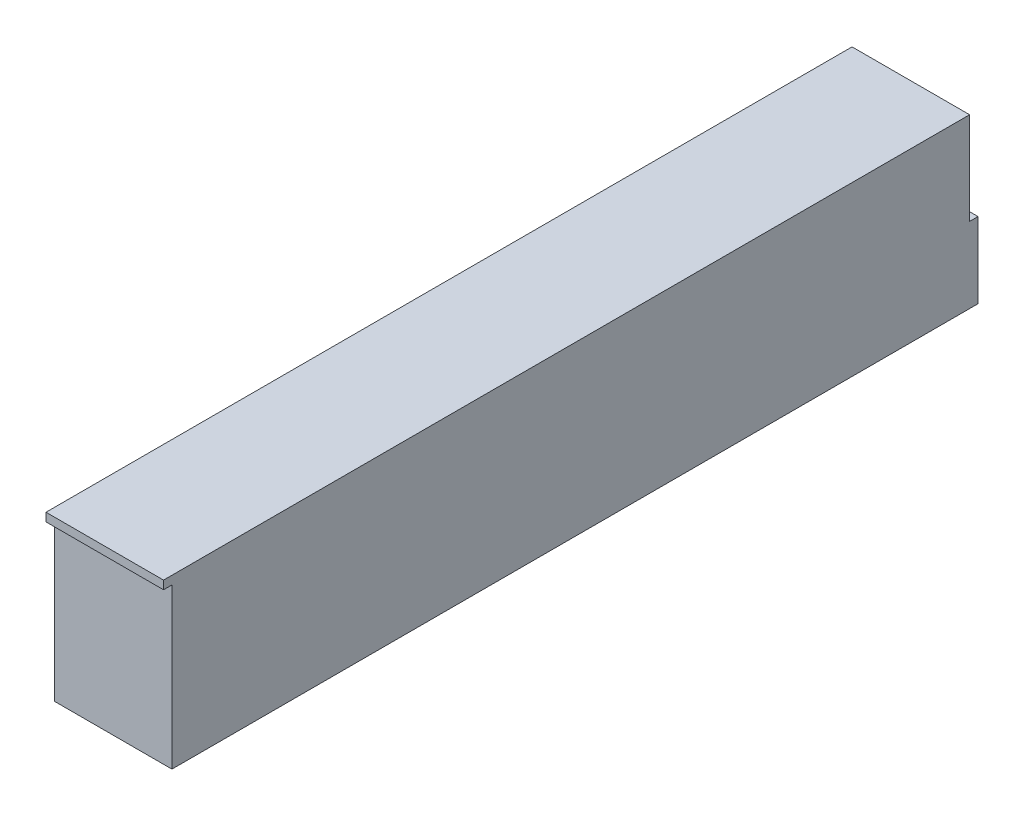
SolidWorks part; units mm, degrees
material "PE High Density Film"
ref_plane "Front Plane" through (0, 0, 0) normal (0, 0, 1) x (1, 0, 0)
ref_plane "Top Plane" through (0, 0, 0) normal (0, 1, 0) x (1, 0, 0)
ref_plane "Right Plane" through (0, 0, 0) normal (1, 0, 0) x (0, 0, -1)
sketch "Sketch1" plane through (0, 0, 0) normal (0, 1, 0) x (1, 0, 0)
  line L0 (0, 0) -> (0, 152.4)
  line L1 (0, 152.4) -> (22.225, 152.4)
  line L2 (22.225, 152.4) -> (22.225, 0)
  line L3 (22.225, 0) -> (0, 0)
  dimension "D1" = 152.4
  dimension "D2" = 22.225
extrude "Boss-Extrude1" add sketch "Sketch1" along normal blind 31.75
sketch "Sketch2" plane through (22.225, 0, 0) normal (1, 0, 0) x (0, 0, -1)
  line L0 (0, 31.75) -> (152.4, 31.75) construction
  line L1 (0, 0) -> (1.5875, 0)
  line L2 (0, 0) -> (0, 30.1625)
  line L3 (0, 30.1625) -> (1.5875, 30.1625)
  line L4 (1.5875, 0) -> (1.5875, 30.1625)
  dimension "D1" = 1.5875
  dimension "D2" = 1.5875
extrude "Cut-Extrude1" cut sketch "Sketch2" against normal through all
sketch "Sketch3" plane through (22.225, 0, 0) normal (1, 0, 0) x (0, 0, -1)
  line L1 (152.4, 0) -> (153.9875, 0)
  line L2 (152.4, 0) -> (152.4, 14.2875)
  line L3 (152.4, 14.2875) -> (153.9875, 14.2875)
  line L4 (153.9875, 0) -> (153.9875, 14.2875)
  dimension "D1" = 14.2875
  dimension "D2" = 1.5875
extrude "Boss-Extrude2" add sketch "Sketch3" against normal up to surface (22.225 mm away) up to face at (0, 20.6375, -51.3292)
